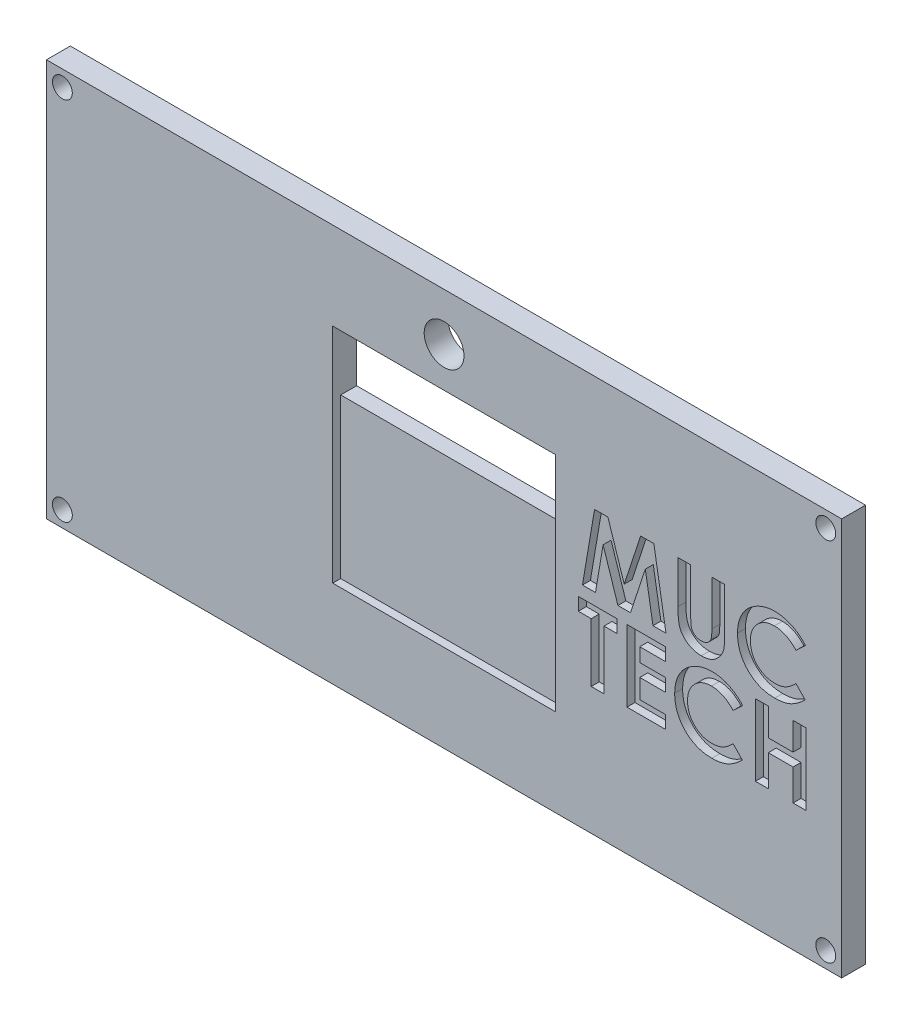
SolidWorks part; units mm, degrees
ref_plane "Ebene vorne" through (0, 0, 0) normal (0, 0, 1) x (1, 0, 0)
ref_plane "Ebene oben" through (0, 0, 0) normal (0, 1, 0) x (1, 0, 0)
ref_plane "Ebene rechts" through (0, 0, 0) normal (1, 0, 0) x (0, 0, -1)
sketch "Skizze1" plane through (0, 0, 0) normal (0, 0, 1) x (1, 0, 0)
  line L0 (-119.1041, 0) -> (126.201, 0) construction
  line L1 (0, -85.0062) -> (0, 96.3063) construction
  line L3 (-50, 25) -> (50, 25)
  line L4 (-50, 25) -> (-50, -25)
  line L5 (-50, -25) -> (50, -25)
  line L6 (50, 25) -> (50, -25)
  dimension "D1" = 50
  dimension "D2" = 100
extrude "Aufsatz-Linear austragen1" add sketch "Skizze1" along normal blind 3 contours L3 L6 L5 L4
sketch "Skizze2" plane through (0, 0, 3) normal (0, 0, 1) x (1, 0, 0)
  line L0 (-50, 0) -> (50, 0) construction
  line L1 (-50, 25) -> (-50, -25) construction
  line L2 (50, 25) -> (50, -25) construction
  line L3 (0, 25) -> (0, -25) construction
  line L4 (-50, 25) -> (50, 25) construction
  line L5 (-50, -25) -> (50, -25) construction
  line L7 (-14, 14) -> (14, 14)
  line L8 (-14, 14) -> (-14, -14)
  line L9 (-14, -14) -> (14, -14)
  line L10 (14, 14) -> (14, -14)
  dimension "D1" = 28
extrude "Schnitt-Linear austragen1" cut sketch "Skizze2" against normal blind 1
sketch "Skizze3" plane through (0, 0, 2) normal (0, 0, 1) x (1, 0, 0)
  line L0 (14, -14) -> (14, 14) construction
  line L1 (-14, 14) -> (14, 14)
  line L2 (-14, 14) -> (-14, 6)
  line L3 (-14, 6) -> (14, 6)
  line L4 (14, 14) -> (14, 6)
  dimension "D1" = 8
extrude "Schnitt-Linear austragen2" cut sketch "Skizze3" against normal through all
hole_wizard "Ø2.5 (2.5) Durchmesser Bohrung1" positions "Skizze4" profile "Skizze5" hole size "Ø2.5" standard "ANSI Metrisch" end condition through all
sketch "Skizze4" plane through (0, 0, 3) normal (0, 0, 1) x (1, 0, 0)
  line L0 (-50, 25) -> (-50, -25) construction
  line L1 (-50, 25) -> (50, 25) construction
  line L2 (0, 25) -> (0, -25) construction
  line L3 (-50, -25) -> (50, -25) construction
  line L5 (-50, 0) -> (50, 0) construction
  line L6 (50, 25) -> (50, -25) construction
  point P1 (-48, 23)
  point P26 (48, 23)
  point P27 (48, -23)
  point P28 (-48, -23)
  dimension "D1" = 2
  dimension "D2" = 2
sketch "Skizze5" plane through (-48, 23, 3) normal (1, 0, 0) x (0, -1, 0)
  line L0 (0, 0) -> (0, 3)
  line L1 (0, 3) -> (1.25, 3)
  line L2 (1.25, 3) -> (1.25, 0)
  line L5 (1.25, 0) -> (0, 0)
  line L11 (0, -6.35) -> (0, 107.95) construction
  dimension "Bohrerdurchmesser" = 2.5
  dimension "Bohrungstiefe" = 3
sketch "Skizze7" plane through (0, 0, 3) normal (0, 0, 1) x (1, 0, 0)
  line L7 (14, 1.5) -> (50, 1.5) construction
  line L8 (14, -14) -> (14, 14) construction
  line L9 (50, 25) -> (50, -25) construction
  line L10 (14, -9) -> (50, -9) construction
  line L11 (14, 14) -> (-14, 14) construction
  text T0 "<b>TECH</b>" font "Century Gothic" height 9
  text T1 "<b>MUC</b>" font "Century Gothic" height 9
  dimension "D2" = 12.5
  dimension "D3" = 5
  dimension "D4" = 10.5
extrude "Schnitt-Linear austragen3" cut sketch "Skizze7" against normal blind 1
hole_wizard "Ø5.0 (5) Durchmesser Bohrung1" positions "Skizze8" profile "Skizze9" hole size "Ø5.0" standard "ANSI Metrisch" end condition through all
sketch "Skizze8" plane through (0, 0, 3) normal (0, 0, 1) x (1, 0, 0)
  line L3 (14, 14) -> (-14, 14) construction
  line L4 (0, 0) -> (0, 25) construction
  line L5 (-50, 25) -> (50, 25) construction
  point P0 (0, 19)
  point P23 (0, 0)
  dimension "D1" = 5
sketch "Skizze9" plane through (0, 19, 3) normal (1, 0, 0) x (0, -1, 0)
  line L0 (0, 0) -> (0, 3)
  line L1 (0, 3) -> (2.5, 3)
  line L2 (2.5, 3) -> (2.5, 0)
  line L5 (2.5, 0) -> (0, 0)
  line L11 (0, -6.35) -> (0, 107.95) construction
  dimension "Bohrerdurchmesser" = 5
  dimension "Bohrungstiefe" = 3
